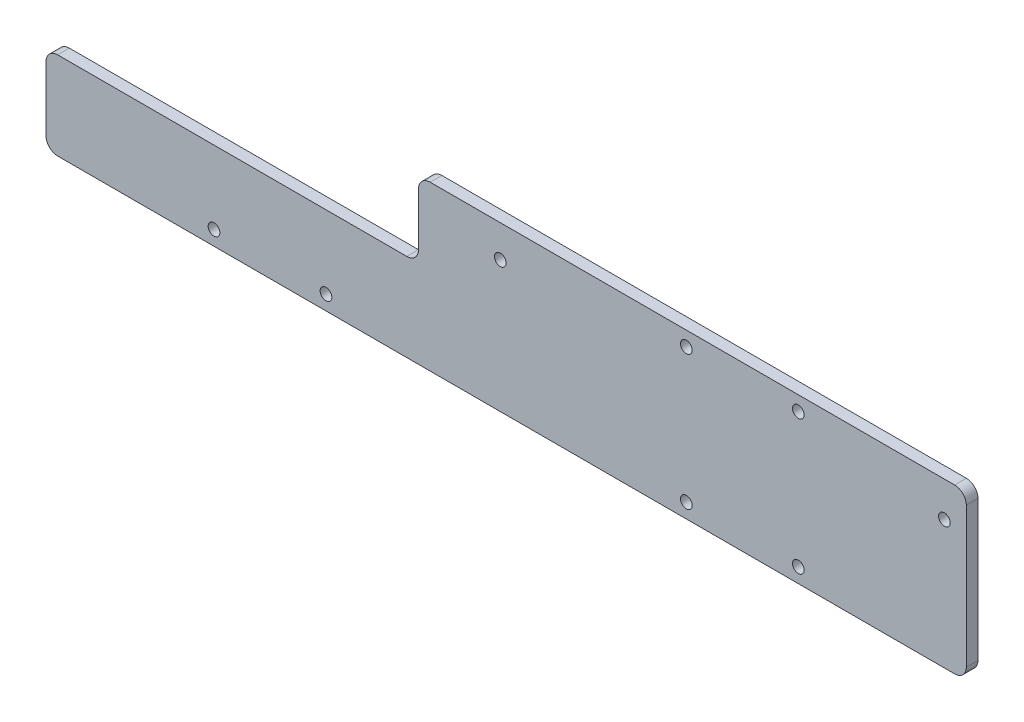
SolidWorks part; units mm, degrees
ref_plane "前视基准面" through (0, 0, 0) normal (0, 0, 1) x (1, 0, 0)
ref_plane "上视基准面" through (0, 0, 0) normal (0, 1, 0) x (1, 0, 0)
ref_plane "右视基准面" through (0, 0, 0) normal (1, 0, 0) x (0, 0, -1)
sketch "草图1" plane through (0, 0, 0) normal (0, 0, 1) x (1, 0, 0)
  line L0 (-27.1941, 11.0961) -> (-27.1941, -12.4101) construction
  line L1 (126.3059, -12.4101) -> (-180.6941, -12.4101)
  line L2 (130.3059, -8.4101) -> (130.3059, 7.7119)
  line L3 (-37.1941, 17.5899) -> (-180.6941, 17.5899)
  line L4 (-184.6941, -8.4101) -> (-184.6941, 13.5899)
  line L5 (130.3059, -12.4101) -> (-184.6941, 17.5899) construction
  line L6 (72.7628, 4.8891) -> (-184.6941, -12.4101) construction
  line L7 (130.3059, 17.5899) -> (130.3059, 7.7119)
  line L10 (-23.1941, 43.5899) -> (126.3059, 43.5899)
  line L11 (130.3059, 17.5899) -> (130.3059, 39.5899)
  line L13 (-27.1941, 39.5899) -> (-27.1941, 27.5899)
  circle A0 centre (-127.1941, -7.4101) radius 2
  circle A1 centre (-88.8641, -7.4101) radius 2
  circle A2 centre (34.4759, -7.4101) radius 2
  circle A3 centre (72.8059, -7.4101) radius 2
  arc A4 (126.3059, -12.4101) -> (130.3059, -8.4101) centre (126.3059, -8.4101) ccw
  arc A6 (-180.6941, -12.4101) -> (-184.6941, -8.4101) centre (-180.6941, -8.4101) cw
  arc A7 (-184.6941, 13.5899) -> (-180.6941, 17.5899) centre (-180.6941, 13.5899) cw
  arc A8 (130.3059, 39.5899) -> (126.3059, 43.5899) centre (126.3059, 39.5899) ccw
  arc A9 (-23.1941, 43.5899) -> (-27.1941, 39.5899) centre (-23.1941, 39.5899) ccw
  circle A11 centre (34.4759, 38.5899) radius 2
  circle A12 centre (72.8059, 38.5899) radius 2
  circle A13 centre (122.8059, 31.5899) radius 2
  arc A14 (-37.1941, 17.5899) -> (-27.1941, 27.5899) centre (-37.1941, 27.5899) ccw
  point P0 (0, 0)
  point P33 (130.3059, 43.5899)
  point P36 (-27.1941, 43.5899)
  dimension "D3" = 4
  dimension "D4" = 4
  dimension "D5" = 38.33
  dimension "D6" = 5
  dimension "D7" = 200
  dimension "D8" = 4
  dimension "D9" = 4
  dimension "D10" = 4
  dimension "D11" = 4
  dimension "D12" = 46
  dimension "D13" = 46
  dimension "D15" = 4
  dimension "D16" = 7.5
  dimension "D17" = 44
  dimension "D18" = 10
  dimension "D1" = 157.5
  dimension "300" = 315
  dimension "D2" = 30
  dimension "D14" = 56
extrude "凸台-拉伸1" add sketch "草图1" along normal blind 4
sketch "草图2" plane through (0, 0, 0) normal (0, 0, -1) x (-1, 0, 0)
  line L0 (37.1941, 17.5899) -> (180.6941, 17.5899) construction
  line L1 (23.1941, 43.5899) -> (53.1941, 43.5899)
  line L2 (23.1941, 43.5899) -> (23.1941, 17.5899)
  line L3 (23.1941, 17.5899) -> (57.1941, 17.5899)
  line L4 (57.1941, 39.5899) -> (57.1941, 21.5899)
  line L5 (61.1941, 17.5899) -> (83.3103, 17.5899)
  line L6 (57.1941, 17.5899) -> (61.1941, 17.5899)
  arc A0 (61.1941, 17.5899) -> (57.1941, 21.5899) centre (61.1941, 21.5899) cw
  arc A1 (57.1941, 39.5899) -> (53.1941, 43.5899) centre (53.1941, 39.5899) ccw
  dimension "D1" = 4
  dimension "D2" = 30
extrude "凸台-拉伸3" add sketch "草图2" against normal blind 4
sketch "草图7" plane through (0, 0, 0) normal (0, 0, -1) x (-1, 0, 0)
  line L0 (-126.3059, -12.4101) -> (180.6941, -12.4101) construction
  line L1 (57.1941, 39.5899) -> (57.1941, 21.5899) construction
  circle A0 centre (29.1941, 32.5899) radius 2
  dimension "D1" = 4
  dimension "D2" = 45
  dimension "D3" = 28
extrude "切除-拉伸2" cut sketch "草图7" against normal blind 10
